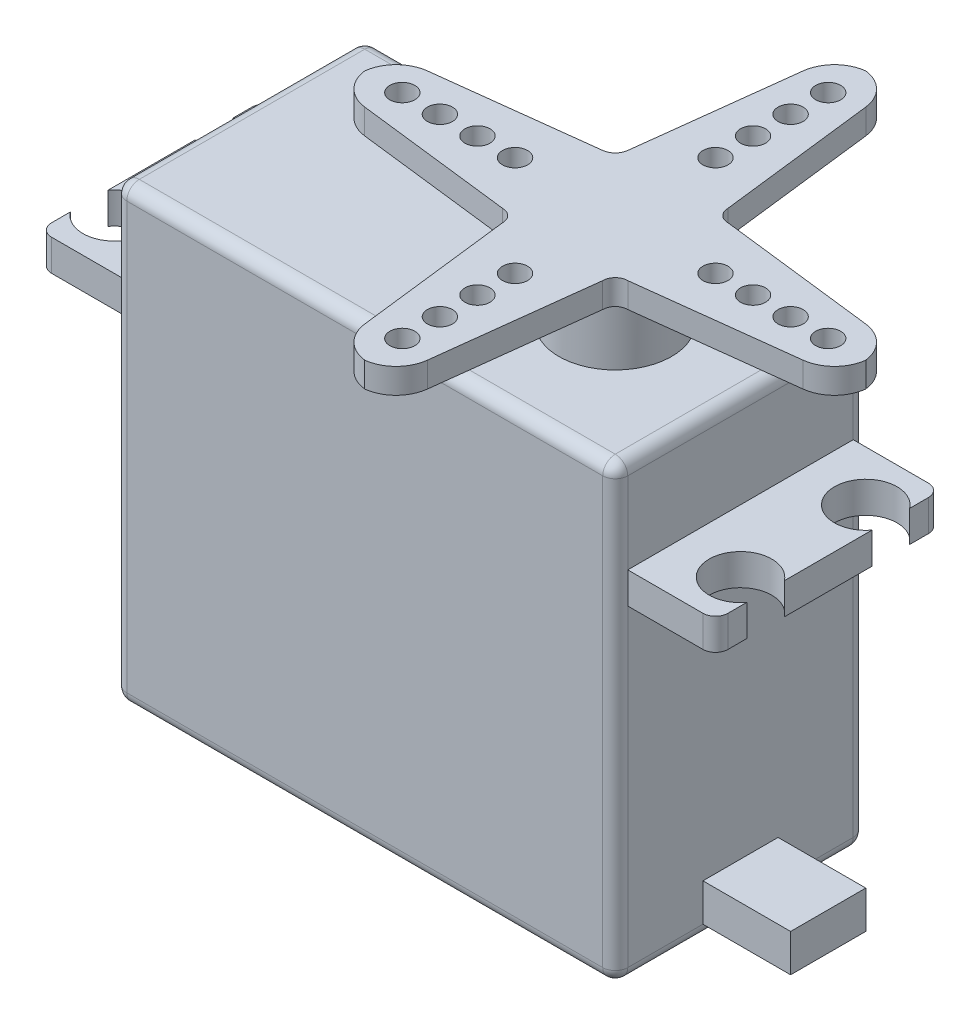
SolidWorks part; units mm, degrees
ref_plane "Front Plane" through (0, 0, 0) normal (0, 0, 1) x (1, 0, 0)
ref_plane "Top Plane" through (0, 0, 0) normal (0, 1, 0) x (1, 0, 0)
ref_plane "Right Plane" through (0, 0, 0) normal (1, 0, 0) x (0, 0, -1)
sketch "Sketch2" plane through (0, 0, 0) normal (0, 1, 0) x (1, 0, 0)
  line L1 (0, 0) -> (40, 0)
  line L2 (0, 0) -> (0, 20)
  line L3 (0, 20) -> (40, 20)
  line L4 (40, 0) -> (40, 20)
extrude "Boss-Extrude1" add sketch "Sketch2" along normal blind 36
fillet "Fillet1" radius 1 12 edges at (40, 0, -10) (40, 18, -20) (20, 0, -20) (40, 18, 0) (20, 0, 0) (0, 18, -20) (0, 18, 0) (0, 0, -10) (20, 36, -20) (40, 36, -10) (20, 36, 0) (0, 36, -10)
sketch "Sketch4" plane through (40, 0, 0) normal (1, 0, 0) x (0, 0, -1)
  line L0 (19, 1) -> (19, 35) construction
  line L1 (19, 26) -> (1, 26)
  line L2 (19, 26) -> (19, 28.5)
  line L3 (19, 28.5) -> (1, 28.5)
  line L4 (1, 26) -> (1, 28.5)
  line L5 (1, 35) -> (1, 1) construction
  line L6 (19, 0) -> (1, 0) construction
  dimension "D1" = 26
  dimension "D2" = 2.5
extrude "Boss-Extrude2" add sketch "Sketch4" along normal blind 7
sketch "Sketch5" plane through (0, 28.5, 0) normal (0, 1, 0) x (1, 0, 0)
  line L0 (47, 1) -> (40, 1) construction
  line L1 (40, 19) -> (40, 1) construction
  line L2 (47, 19) -> (40, 19) construction
  circle A0 centre (45, 5) radius 2.5
  circle A1 centre (45, 15) radius 2.5
  dimension "D1" = 4
  dimension "D3" = 4
  dimension "D2" = 5
extrude "Cut-Extrude1" cut sketch "Sketch5" against normal up to next
fillet "Fillet2" radius 1 2 edges at (47, 27.25, -1) (47, 27.25, -19)
sketch "Sketch7" plane through (0, 0, 0) normal (-1, 0, 0) x (0, 0, 1)
  line L0 (-19, 35) -> (-19, 1) construction
  line L1 (-19, 26) -> (-1, 26)
  line L2 (-19, 26) -> (-19, 28.5)
  line L3 (-19, 28.5) -> (-1, 28.5)
  line L4 (-1, 26) -> (-1, 28.5)
  line L5 (-1, 1) -> (-1, 35) construction
  line L6 (-1, 0) -> (-19, 0) construction
  dimension "D1" = 26
  dimension "D2" = 2.5
extrude "Boss-Extrude3" add sketch "Sketch7" along normal blind 7
fillet "Fillet3" radius 1 2 edges at (-7, 27.25, -19) (-7, 27.25, -1)
sketch "Sketch8" plane through (0, 28.5, 0) normal (0, 1, 0) x (1, 0, 0)
  line L0 (-6, 19) -> (0, 19) construction
  line L1 (0, 1) -> (0, 19) construction
  line L2 (-6, 1) -> (0, 1) construction
  circle A0 centre (-5, 15) radius 2.5
  circle A1 centre (-5, 5) radius 2.5
  dimension "D1" = 4
  dimension "D3" = 4
  dimension "D2" = 5
extrude "Cut-Extrude2" cut sketch "Sketch8" against normal up to next
sketch "Sketch9" plane through (0, 36, 0) normal (0, 1, 0) x (1, 0, 0)
  line L0 (1, 10) -> (39, 10) construction
  line L1 (1, 19) -> (1, 1) construction
  line L2 (39, 1) -> (39, 19) construction
  line L4 (40, 19) -> (40, 1) construction
  circle A0 centre (30, 10) radius 4.5
  dimension "D1" = 10
extrude "Boss-Extrude4" add sketch "Sketch9" along normal blind 5.5
sketch "Sketch10" plane through (0, 41.5, 0) normal (0, 1, 0) x (1, 0, 0)
  line L12 (30, -10) -> (30, 30) construction
  line L13 (50, 10) -> (10, 10) construction
  line L14 (27.5, 27.5) -> (26, 15)
  line L15 (25, 14) -> (12.5, 12.5)
  line L16 (12.5, 7.5) -> (25, 6)
  line L17 (26, 5) -> (27.5, -7.5)
  line L18 (32.5, -7.5) -> (34, 5)
  line L19 (35, 6) -> (47.5, 7.5)
  line L20 (47.5, 12.5) -> (35, 14)
  line L21 (32.5, 27.5) -> (34, 15)
  arc A0 (27.5, 27.5) -> (30, 30) centre (30.3409, 27.1591) cw
  arc A1 (32.5, 27.5) -> (30, 30) centre (29.6591, 27.1591) ccw
  arc A2 (12.5, 12.5) -> (10, 10) centre (12.8409, 9.6591) ccw
  arc A3 (12.5, 7.5) -> (10, 10) centre (12.8409, 10.3409) cw
  arc A4 (27.5, -7.5) -> (30, -10) centre (30.3409, -7.1591) ccw
  arc A5 (32.5, -7.5) -> (30, -10) centre (29.6591, -7.1591) cw
  arc A6 (47.5, 12.5) -> (50, 10) centre (47.1591, 9.6591) cw
  arc A7 (26, 15) -> (25, 14) centre (24.8636, 15.1364) cw
  arc A8 (34, 15) -> (35, 14) centre (35, 15) ccw
  arc A9 (35, 6) -> (34, 5) centre (35, 5) ccw
  arc A10 (26, 5) -> (25, 6) centre (25, 5) ccw
  arc A11 (47.5, 7.5) -> (50, 10) centre (47.1591, 10.3409) ccw
  point P12 (25, 15)
  point P13 (25, 5)
  point P14 (35, 5)
  point P15 (35, 15)
extrude "Boss-Extrude5" add sketch "Sketch10" along normal blind 2
sketch "Sketch11" plane through (0, 43.5, 0) normal (0, 1, 0) x (1, 0, 0)
  line L0 (30, 30) -> (30, -10) construction
  line L1 (10, 10) -> (50, 10) construction
  circle A0 centre (30, 27) radius 1
  circle A1 centre (30, 24) radius 1
  circle A2 centre (30, 21) radius 1
  circle A3 centre (30, 18) radius 1
  circle A4 centre (47, 10) radius 1
  circle A5 centre (44, 10) radius 1
  circle A6 centre (41, 10) radius 1
  circle A7 centre (38, 10) radius 1
  circle A8 centre (30, -7) radius 1
  circle A9 centre (30, -4) radius 1
  circle A10 centre (30, -1) radius 1
  circle A11 centre (30, 2) radius 1
  circle A12 centre (13, 10) radius 1
  circle A13 centre (16, 10) radius 1
  circle A14 centre (19, 10) radius 1
  circle A15 centre (22, 10) radius 1
  point P16 (30, 10)
  point P27 (30, 10)
  point P36 (30, 10)
  point P45 (30, 10)
  dimension "D1" = 3
  dimension "D2" = 3
  dimension "D3" = 3
  dimension "D4" = 3
  dimension "D5" = 4
extrude "Cut-Extrude3" cut sketch "Sketch11" against normal up to next
sketch "Sketch12" plane through (40, 0, 0) normal (1, 0, 0) x (0, 0, -1)
  line L0 (10, 1) -> (10, 35) construction
  line L1 (1, 1) -> (19, 1) construction
  line L2 (19, 35) -> (1, 35) construction
  line L3 (1, 26) -> (1, 1) construction
  line L4 (7, 4) -> (13, 4)
  line L5 (7, 4) -> (7, 1)
  line L6 (7, 1) -> (13, 1)
  line L7 (13, 4) -> (13, 1)
  line L8 (7, 4) -> (13, 1) construction
  line L9 (7, 1) -> (13, 4) construction
  point P6 (10, 2.5)
  dimension "D1" = 6
  dimension "D2" = 3
extrude "Boss-Extrude6" add sketch "Sketch12" along normal blind 7
